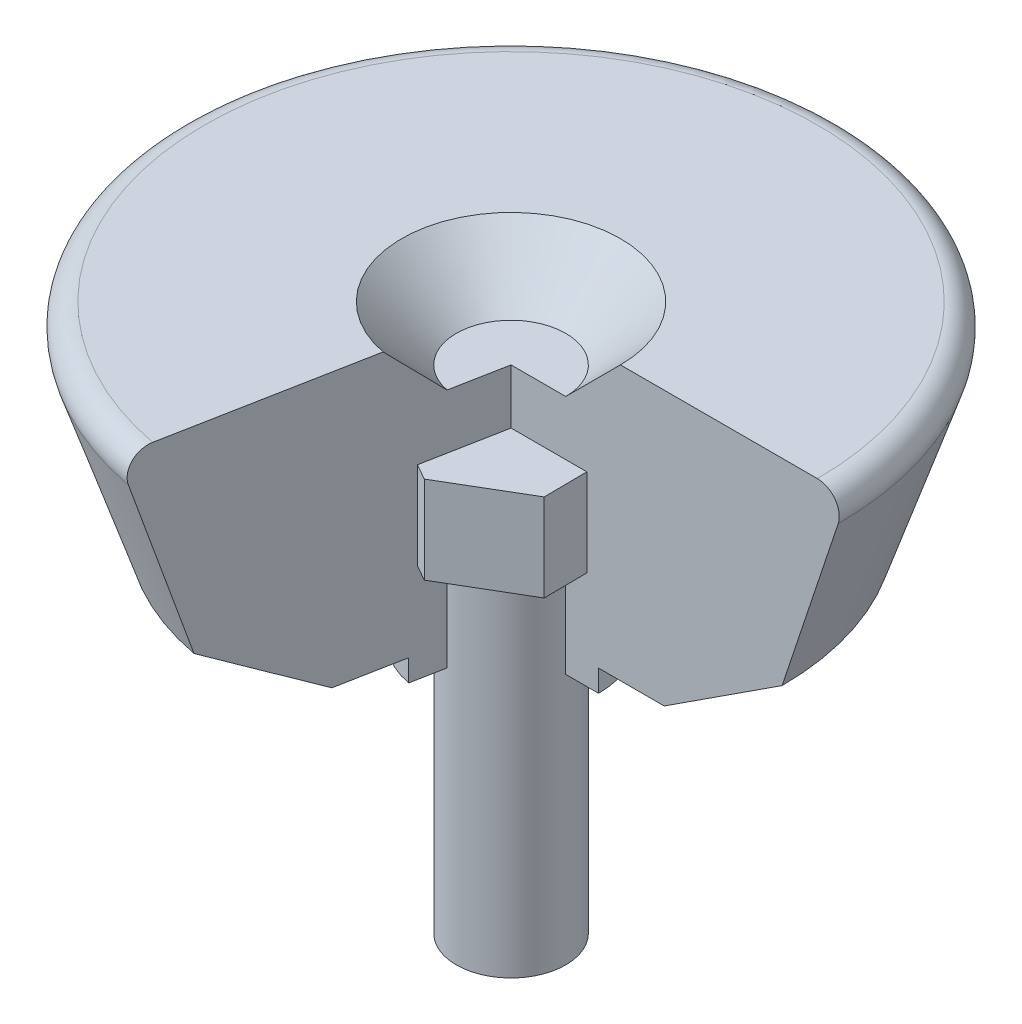
SolidWorks part; units mm, degrees
ref_plane "Спереди" through (0, 0, 0) normal (0, 0, 1) x (1, 0, 0)
ref_plane "Сверху" through (0, 0, 0) normal (0, 1, 0) x (1, 0, 0)
ref_plane "Справа" through (0, 0, 0) normal (1, 0, 0) x (0, 0, -1)
ref_plane "Y" through (0, 0, 0) normal (0, 1, 0) x (1, 0, 0)
ref_plane "X" through (0, 0, 0) normal (1, 0, 0) x (0, 0, -1)
ref_plane "Z" through (0, 0, 0) normal (0, 0, 1) x (1, 0, 0)
ref_plane "Плоскость4" through (0, 0, 0) normal (0, 0, 1) x (1, 0, 0)
sketch "Эскиз1" plane through (0, 0, 0) normal (0, 0, 1) x (1, 0, 0)
  point P0 (0, 0)
ref_plane "Плоскость5" through (0, 0, 0) normal (0, 0, 1) x (1, 0, 0)
sketch "Эскиз2" plane through (0, 0, 0) normal (0, 0, 1) x (1, 0, 0)
  point P0 (0, 60)
ref_axis "Ось1" through (0, 0, 0) along (0, 1, 0)
ref_plane "mate" through (0, 0, 0) normal (0, 0, 1) x (1, 0, 0)
sketch "Эскиз3" plane through (0, 0, 0) normal (0, 0, 1) x (1, 0, 0)
  line L0 (8, 10) -> (8, 12)
  line L1 (8, 12) -> (8, 27)
  line L2 (10, 25) -> (8, 25)
  line L3 (8, 25) -> (8, 10)
sketch "Эскиз4" plane through (0, 0, 0) normal (0, 0, 1) x (1, 0, 0)
  line L0 (0, 23) -> (8, 23)
  line L1 (0, 0) -> (0, 60) construction
  line L2 (8, 12) -> (8, 27) construction
  line L3 (8, 23) -> (8, 25)
  line L4 (8, 25) -> (14, 25)
  line L5 (14, 25) -> (24.7749, 32)
  line L6 (24.7749, 32) -> (29.8974, 47.3675)
  line L7 (28, 50) -> (0, 50)
  line L8 (0, 50) -> (0, 23)
  arc A0 (28, 50) -> (29.8974, 47.3675) centre (28, 48) cw
  dimension "D1" = 2
  dimension "D2" = 23
  dimension "D3" = 2
  dimension "D4" = 25
  dimension "D5" = 28
revolve "Повернуть2" add sketch "Эскиз4" angle 259.2 about axis through (0, 0, 0) along (0, 1, 0)
ref_plane "Плоскость7" through (0, 50, 0) normal (0, 1, 0) x (1, 0, 0)
sketch "Эскиз5" plane through (0, 50, 0) normal (0, 1, 0) x (1, 0, 0)
  circle A0 centre (0, 0) radius 10
ref_plane "Плоскость8" through (0, 45, 0) normal (0, 1, 0) x (1, 0, 0)
sketch "Эскиз6" plane through (0, 45, 0) normal (0, 1, 0) x (1, 0, 0)
  circle A0 centre (0, 0) radius 5
loft "Вырез-По сечениям1" cut profiles "Эскиз5", "Эскиз6"
ref_plane "Плоскость9" through (0, 40, 0) normal (0, 1, 0) x (1, 0, 0)
sketch "Эскиз7" plane through (0, 40, 0) normal (0, 1, 0) x (1, 0, 0)
  line L1 (-0.0731, 7.9997) -> (-6.9645, 3.9365)
  line L2 (-6.9645, 3.9365) -> (-6.8914, -4.0631)
  line L3 (-6.8914, -4.0631) -> (0.0731, -7.9997)
  line L4 (0.0731, -7.9997) -> (6.9645, -3.9365)
  line L5 (6.9645, -3.9365) -> (6.8914, 4.0631)
  line L6 (6.8914, 4.0631) -> (-0.0731, 7.9997)
  circle A0 centre (0, 0) radius 6.9282 construction
extrude "Бобышка-Вытянуть1" add sketch "Эскиз7" against normal blind 8 separate body
ref_plane "Плоскость10" through (0, 32, 0) normal (0, 1, 0) x (1, 0, 0)
sketch "Эскиз8" plane through (0, 32, 0) normal (0, 1, 0) x (1, 0, 0)
  circle A0 centre (0, 0) radius 5
extrude "Бобышка-Вытянуть2" add sketch "Эскиз8" against normal blind 32 separate body
